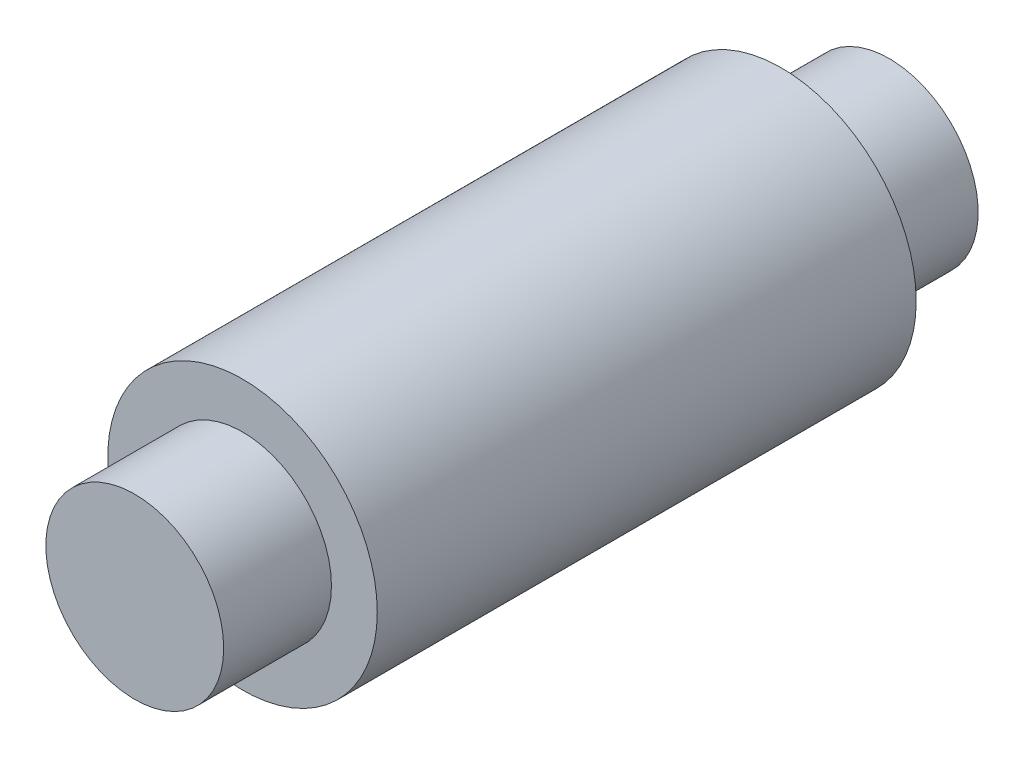
SolidWorks part; units mm, degrees
ref_plane "Plan de face" through (0, 0, 0) normal (0, 0, 1) x (1, 0, 0)
ref_plane "Plan de dessus" through (0, 0, 0) normal (0, 1, 0) x (1, 0, 0)
ref_plane "Plan de droite" through (0, 0, 0) normal (1, 0, 0) x (0, 0, -1)
sketch "Esquisse1" plane through (0, 0, 0) normal (0, 0, 1) x (1, 0, 0)
  circle A0 centre (0, 0) radius 2.5
  dimension "D1" = 5
extrude "Boss.-Extru.1" add sketch "Esquisse1" along normal blind 10
sketch "Esquisse2" plane through (0, 0, 10) normal (0, 0, 1) x (1, 0, 0)
  circle A0 centre (0, 0) radius 1.65
  dimension "D1" = 3.3
extrude "Boss.-Extru.2" add sketch "Esquisse2" along normal blind 2
sketch "Esquisse3" plane through (0, 0, 0) normal (0, 0, -1) x (-1, 0, 0)
  circle A0 centre (0, 0) radius 1.65
  dimension "D1" = 3.3
extrude "Boss.-Extru.3" add sketch "Esquisse3" along normal blind 2
